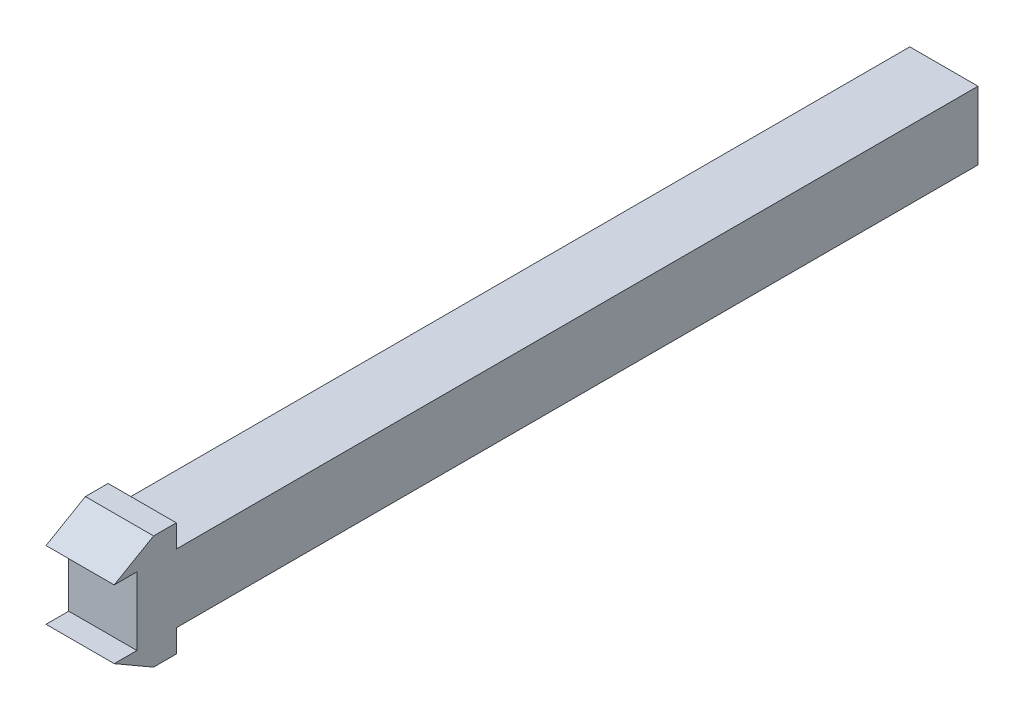
SolidWorks part; units mm, degrees
ref_plane "Front Plane" through (0, 0, 0) normal (0, 0, 1) x (1, 0, 0)
ref_plane "Top Plane" through (0, 0, 0) normal (0, 1, 0) x (1, 0, 0)
ref_plane "Right Plane" through (0, 0, 0) normal (1, 0, 0) x (0, 0, -1)
sketch "Sketch1" plane through (0, 0, 0) normal (0, 0, 1) x (1, 0, 0)
  line L1 (-7.5, -7.5) -> (7.5, -7.5)
  line L2 (-7.5, -7.5) -> (-7.5, 7.5)
  line L3 (-7.5, 7.5) -> (7.5, 7.5)
  line L4 (7.5, -7.5) -> (7.5, 7.5)
  line L5 (-7.5, -7.5) -> (7.5, 7.5) construction
  line L6 (-7.5, 7.5) -> (7.5, -7.5) construction
  point P0 (0, 0)
  dimension "D1" = 15
  dimension "D2" = 15
extrude "Boss-Extrude1" add sketch "Sketch1" along normal blind 190
sketch "Sketch2" plane through (-7.5, 0, 0) normal (-1, 0, 0) x (0, 0, 1)
  line L0 (190, 7.5) -> (181.3397, 12.5)
  line L1 (181.3397, 12.5) -> (176.3397, 12.5)
  line L2 (176.3397, 12.5) -> (176.3397, 7.5)
  line L3 (190, 7.5) -> (0, 7.5) construction
  line L4 (190, 0) -> (155.7578, 0) construction
  line L5 (190, 7.5) -> (190, -7.5) construction
  line L6 (176.3397, -12.5) -> (176.3397, -7.5)
  line L7 (181.3397, -12.5) -> (176.3397, -12.5)
  line L8 (190, -7.5) -> (181.3397, -12.5)
  line L9 (176.3397, 7.5) -> (190, 7.5)
  line L10 (190, -7.5) -> (176.3397, -7.5)
  dimension "D1" = 30
  dimension "D2" = 5
  dimension "D3" = 5
extrude "Boss-Extrude2" add sketch "Sketch2" against normal up to surface (15 mm away) up to face at (7.5, 0, 95)
sketch "Sketch3" plane through (0, 0, 190) normal (0, 0, 1) x (1, 0, 0)
  line L4 (7.5, -7.5) -> (7.5, 7.5)
  line L5 (7.5, 7.5) -> (-7.5, 7.5)
  line L6 (-7.5, 7.5) -> (-7.5, -7.5)
  line L7 (-7.5, -7.5) -> (7.5, -7.5)
  line L8 (7.5, -7.5) -> (7.5, 7.5)
  line L9 (7.5, 7.5) -> (-7.5, 7.5)
  line L10 (-7.5, 7.5) -> (-7.5, -7.5)
  line L11 (-7.5, -7.5) -> (7.5, -7.5)
  dimension "D1" = 0
extrude "Cut-Extrude1" cut sketch "Sketch3" along direction (0, 0, -1) on the side against the normal blind 5 contours L8 L9 L10 L11
